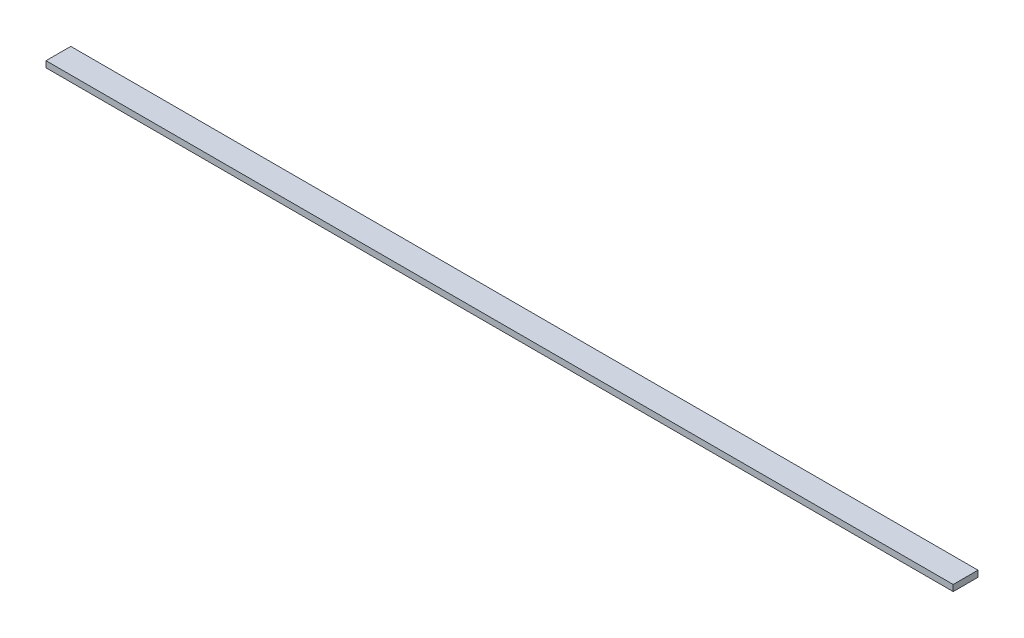
SolidWorks part; units mm, degrees
ref_plane "Front Plane" through (0, 0, 0) normal (0, 0, 1) x (1, 0, 0)
ref_plane "Top Plane" through (0, 0, 0) normal (0, 1, 0) x (1, 0, 0)
ref_plane "Right Plane" through (0, 0, 0) normal (1, 0, 0) x (0, 0, -1)
sketch "Sketch1" plane through (0, 0, 0) normal (0, 1, 0) x (1, 0, 0)
  line L1 (116.205, -3.175) -> (-116.205, -3.175)
  line L2 (116.205, -3.175) -> (116.205, 3.175)
  line L3 (116.205, 3.175) -> (-116.205, 3.175)
  line L4 (-116.205, -3.175) -> (-116.205, 3.175)
  line L5 (116.205, -3.175) -> (-116.205, 3.175) construction
  line L6 (116.205, 3.175) -> (-116.205, -3.175) construction
  point P0 (0, 0)
  dimension "D1" = 6.35
  dimension "D2" = 232.41
extrude "Boss-Extrude1" add sketch "Sketch1" along normal blind 1.5875
